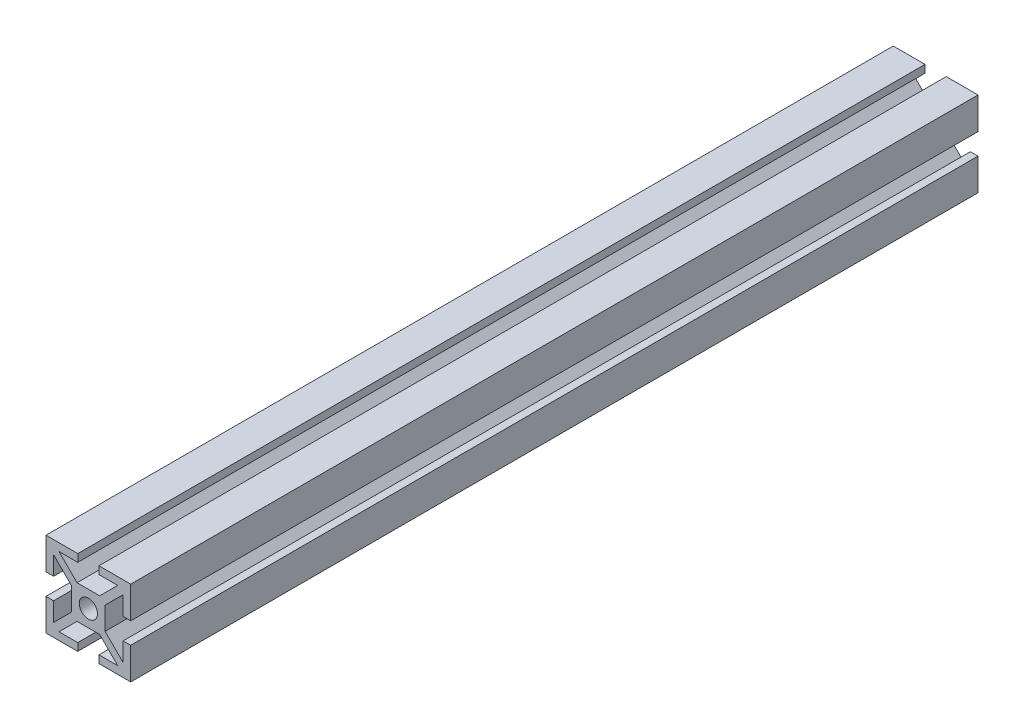
SolidWorks part; units mm, degrees
material "6063-T5"
ref_plane "Front Plane" through (0, 0, 0) normal (0, 0, 1) x (1, 0, 0)
ref_plane "Top Plane" through (0, 0, 0) normal (0, 1, 0) x (1, 0, 0)
ref_plane "Right Plane" through (0, 0, 0) normal (1, 0, 0) x (0, 0, -1)
sketch "Sketch2" plane through (0, 0, 0) normal (0, 0, 1) x (1, 0, 0)
  line L0 (-2.5, 10) -> (-2.5, 8.2)
  line L1 (-10, -10) -> (-2.5, -10)
  line L2 (-10, -10) -> (-10, -2.5)
  line L3 (-10, 10) -> (-2.5, 10)
  line L4 (10, -10) -> (10, -2.5)
  line L5 (-10, -10) -> (10, 10) construction
  line L6 (-10, 10) -> (10, -10) construction
  line L7 (-6.9272, -8.2) -> (-2.5, -8.2)
  line L8 (-8.2, -6.9272) -> (-8.2, -2.5)
  line L9 (-6.9272, 8.2) -> (-2.5, 8.2)
  line L10 (8.2, -6.9272) -> (8.2, -2.5)
  line L13 (2.5, 10) -> (2.5, 8.2)
  line L14 (2.5, 10) -> (10, 10)
  line L15 (2.5, 8.2) -> (6.9272, 8.2)
  line L16 (0, 0) -> (0, 17.5125) construction
  line L17 (-2.15, 2.15) -> (2.15, 2.15) construction
  line L18 (-2.6772, -3.95) -> (2.6772, -3.95)
  line L19 (-3.95, -2.6772) -> (-3.95, 2.6772)
  line L20 (-2.6772, 3.95) -> (2.6772, 3.95)
  line L21 (3.95, -2.6772) -> (3.95, 2.6772)
  line L24 (-2.6772, 3.95) -> (-6.9272, 8.2)
  line L25 (-3.95, 2.6772) -> (-8.2, 6.9272)
  line L26 (10, 2.5) -> (8.2, 2.5)
  line L27 (10, -2.5) -> (8.2, -2.5)
  line L28 (3.95, 2.6772) -> (8.2, 6.9272)
  line L29 (2.6772, 3.95) -> (6.9272, 8.2)
  line L30 (2.5, -10) -> (2.5, -8.2)
  line L31 (-2.5, -10) -> (-2.5, -8.2)
  line L32 (2.6772, -3.95) -> (6.9272, -8.2)
  line L33 (3.95, -2.6772) -> (8.2, -6.9272)
  line L34 (-10, -2.5) -> (-8.2, -2.5)
  line L35 (-10, 2.5) -> (-8.2, 2.5)
  line L36 (-3.95, -2.6772) -> (-8.2, -6.9272)
  line L37 (-2.6772, -3.95) -> (-6.9272, -8.2)
  line L38 (-10, 2.5) -> (-10, 10)
  line L39 (-8.2, 2.5) -> (-8.2, 6.9272)
  line L40 (10, 2.5) -> (10, 10)
  line L41 (8.2, 2.5) -> (8.2, 6.9272)
  line L42 (2.5, -8.2) -> (6.9272, -8.2)
  line L43 (2.5, -10) -> (10, -10)
  circle A0 centre (0, 0) radius 2.15
  point P0 (0, 0)
  point P54 (0, 0)
  dimension "D3" = 4.3
  dimension "D7" = 1.8
  dimension "D1" = 20
  dimension "D4" = 1.8
  dimension "D5" = 5
  dimension "D6" = 1.8
  dimension "D8" = 4
extrude "Boss-Extrude1" add sketch "Sketch2" along normal mid plane 200
